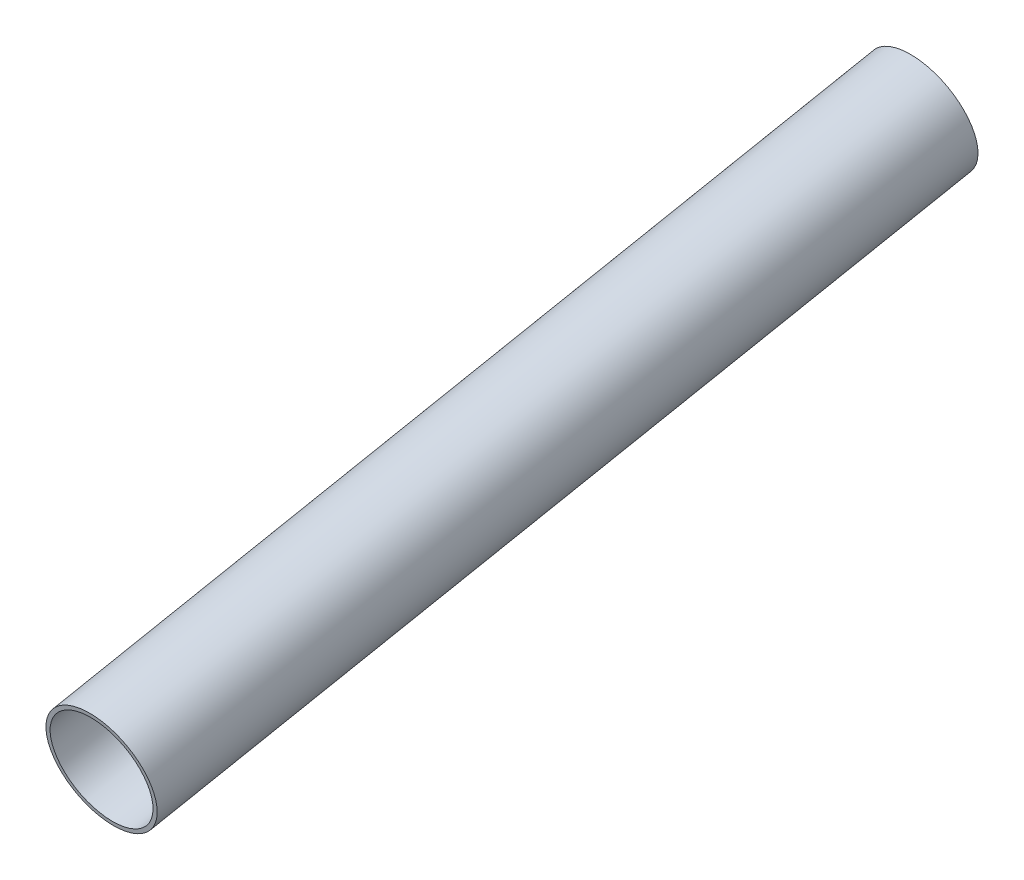
SolidWorks part; units mm, degrees
ref_plane "Front Plane" through (0, 0, 0) normal (0, 0, 1) x (1, 0, 0)
ref_plane "Top Plane" through (0, 0, 0) normal (0, 1, 0) x (1, 0, 0)
ref_plane "Right Plane" through (0, 0, 0) normal (1, 0, 0) x (0, 0, -1)
ref_plane "Plane4" through (-4.3209, 462.86, 1874.607) normal (-0.0089, -0.2018, 0.9794) x (1, -0.0012, 0.0089)
sketch "Sketch1" plane through (-4.3209, 462.86, 1874.607) normal (-0.0089, -0.2018, 0.9794) x (1, -0.0012, 0.0089)
  circle A0 centre (0, 0) radius 9.525
  circle A1 centre (0, 0) radius 8.8138
extrude "Boss-Extrude1" add sketch "Sketch1" against normal up to vertex (92.71 mm away) and the other way up to vertex (51.1175 mm away)
